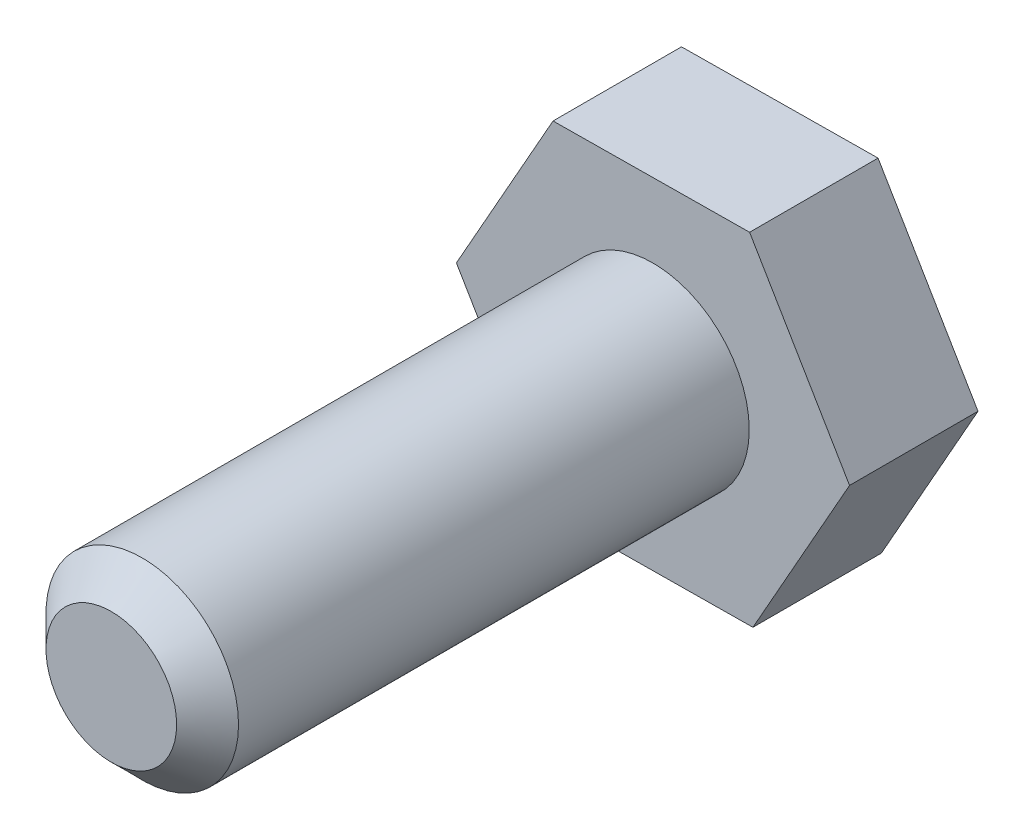
SolidWorks part; units mm, degrees
material "Stop odlewniczy stali"
ref_plane "Front" through (0, 0, 0) normal (0, 0, 1) x (1, 0, 0)
ref_plane "Top" through (0, 0, 0) normal (0, 1, 0) x (1, 0, 0)
ref_plane "Right" through (0, 0, 0) normal (1, 0, 0) x (0, 0, -1)
sketch "Szkic1" plane through (0, 0, 0) normal (0, 0, 1) x (1, 0, 0)
  line L1 (-3.2291, 5.4687) -> (-6.3505, -0.0621)
  line L2 (-6.3505, -0.0621) -> (-3.1215, -5.5308)
  line L3 (-3.1215, -5.5308) -> (3.2291, -5.4687)
  line L4 (3.2291, -5.4687) -> (6.3505, 0.0621)
  line L5 (6.3505, 0.0621) -> (3.1215, 5.5308)
  line L6 (3.1215, 5.5308) -> (-3.2291, 5.4687)
  circle A0 centre (0, 0) radius 5.5 construction
  dimension "D1" = 11
extrude "Dodanie-wyciągnięcie1" add sketch "Szkic1" along normal blind 4.15
sketch "Szkic2" plane through (0, 0, 4.15) normal (0, 0, 1) x (1, 0, 0)
  circle A0 centre (0, 0) radius 3.11
extrude "Dodanie-wyciągnięcie2" add sketch "Szkic2" along normal blind 17.5 contours A0
chamfer "Sfazowanie1" distance 1 angle 45 1 edges at (3.11, 0, 21.65)
